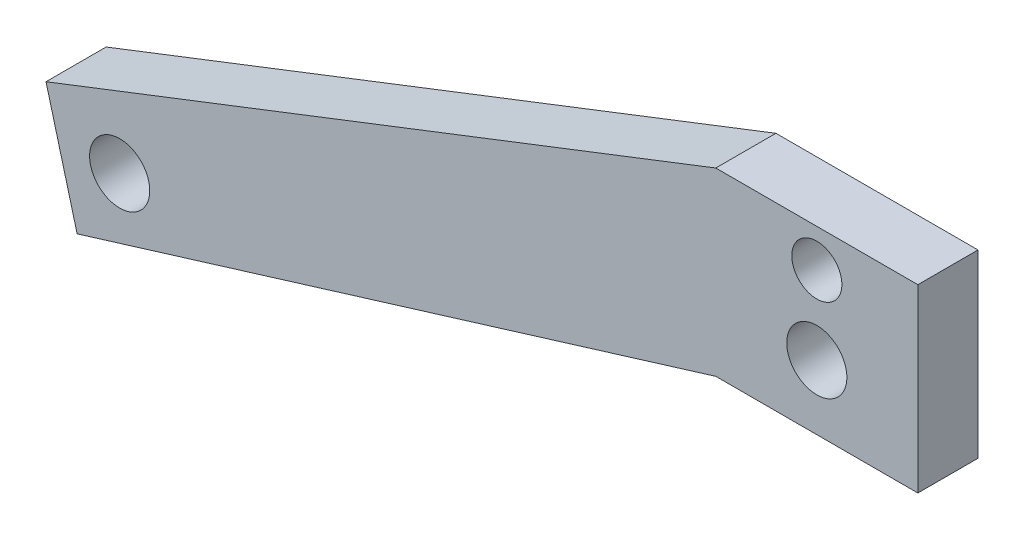
SolidWorks part; units mm, degrees
ref_plane "Front Plane" through (0, 0, 0) normal (0, 0, 1) x (1, 0, 0)
ref_plane "Top Plane" through (0, 0, 0) normal (0, 1, 0) x (1, 0, 0)
ref_plane "Right Plane" through (0, 0, 0) normal (1, 0, 0) x (0, 0, -1)
sketch "Sketch1" plane through (0, 0, 0) normal (0, 0, 1) x (1, 0, 0)
  line L0 (-16, 45) -> (-122.071, 3.7997)
  line L2 (-276.7879, -13.7826) -> (-251.7788, -35.3348) construction
  line L3 (0, 26.6476) -> (-110.4053, -2.9354) construction
  line L4 (-16, 45) -> (-16, 15)
  line L5 (-16, 15) -> (16, 15)
  line L6 (16, 15) -> (16, 45)
  line L7 (16, 45) -> (-16, 45)
  line L8 (-16, 45) -> (-16, 16.425) construction
  line L9 (-16, 15) -> (16, 15) construction
  line L10 (16, 16.425) -> (16, 45)
  line L11 (16, 45) -> (-16, 45)
  line L12 (16, 16.425) -> (-16, 16.425)
  line L13 (-16, 16.425) -> (-117.1405, -14.6011)
  line L14 (-117.1405, -14.6011) -> (-122.071, 3.7997)
  line L15 (-251.7788, -35.3348) -> (-242.2031, -37.4927) construction
  line L17 (-30.7143, 26.228) -> (-28.037, 26.7) construction
  line L18 (-2117.156, -341.6) -> (-28.037, 26.7) construction
  line L19 (-242.2031, -37.4927) -> (-208.8903, -37.4927) construction
  line L20 (-208.8903, -37.4927) -> (-16, 45) construction
  line L21 (-292.5067, -43.5335) -> (-248.9466, -55.1606) construction
  line L22 (-248.9466, -55.1606) -> (-208.8903, -56.2396) construction
  line L23 (-208.8903, -56.2396) -> (-14.9476, 16.425) construction
  line L24 (-288.0555, -26.8574) -> (0, 26.6476) construction
  line L47 (-110.4053, -2.9354) -> (-119.6058, -5.4007) construction
  circle A0 centre (0, 39) radius 3.9688 construction
  circle A1 centre (0, 39) radius 3.9688
  circle A2 centre (0, 26.6476) radius 4.7625
  circle A3 centre (-110.4053, -2.9354) radius 4.7625
  circle A4 centre (-288.0555, -26.8574) radius 17.26 construction
  point P19 (0, 0)
  point P21 (-119.6058, -5.4007)
  point P22 (-37.2984, 17.3696)
  dimension "D2" = 9.525
  dimension "D4" = 114.3
  dimension "D7" = 292.9825
  dimension "D3" = 9.525
  dimension "D5" = 19.05
  dimension "D6" = 28.575
  dimension "D8" = 15
  dimension "D9" = 32
  dimension "D1" = 0
extrude "Boss-Extrude1" add sketch "Sketch1" along normal blind 9.525
